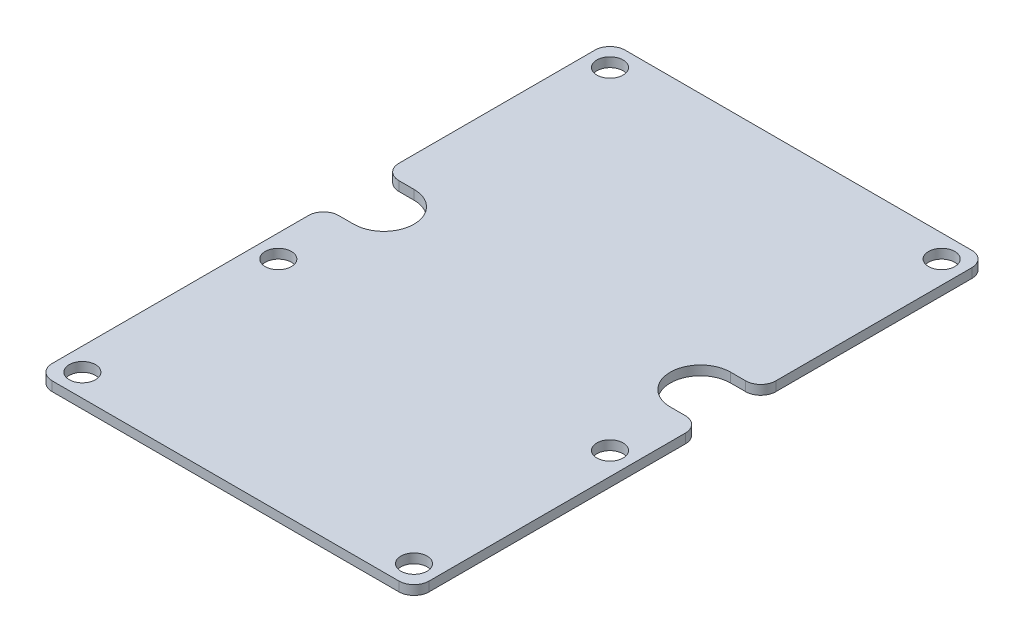
SolidWorks part; units mm, degrees
ref_plane "Front Plane" through (0, 0, 0) normal (0, 0, 1) x (1, 0, 0)
ref_plane "Top Plane" through (0, 0, 0) normal (0, 1, 0) x (1, 0, 0)
ref_plane "Right Plane" through (0, 0, 0) normal (1, 0, 0) x (0, 0, -1)
sketch "Sketch1" plane through (0, 0, 0) normal (0, 1, 0) x (1, 0, 0)
  line L0 (-25.4, -13.97) -> (-25.4, 19.05) construction
  line L1 (22.86, -11.43) -> (-22.86, -11.43) construction
  line L2 (22.86, -11.43) -> (22.86, 11.43) construction
  line L3 (22.86, 11.43) -> (-22.86, 11.43) construction
  line L4 (-22.86, -11.43) -> (-22.86, 11.43) construction
  line L5 (22.86, -11.43) -> (-22.86, 11.43) construction
  line L6 (22.86, 11.43) -> (-22.86, -11.43) construction
  line L7 (-21.59, -12.7) -> (-24.13, -12.7) construction
  line L8 (-21.59, -12.7) -> (-21.59, 12.7) construction
  line L9 (-21.59, 12.7) -> (-24.13, 12.7) construction
  line L10 (-24.13, -12.7) -> (-24.13, 12.7) construction
  line L11 (-21.59, -12.7) -> (-24.13, 12.7) construction
  line L12 (-21.59, 12.7) -> (-24.13, -12.7) construction
  line L13 (24.13, -12.7) -> (21.59, -12.7) construction
  line L14 (24.13, -12.7) -> (24.13, 12.7) construction
  line L15 (24.13, 12.7) -> (21.59, 12.7) construction
  line L16 (21.59, -12.7) -> (21.59, 12.7) construction
  line L17 (24.13, -12.7) -> (21.59, 12.7) construction
  line L18 (24.13, 12.7) -> (21.59, -12.7) construction
  line L19 (-25.4, 19.05) -> (18.415, 19.05) construction
  line L20 (18.415, 19.05) -> (25.4, 12.065) construction
  line L21 (25.4, 12.065) -> (25.4, -13.97) construction
  line L22 (25.4, -13.97) -> (-25.4, -13.97) construction
  line L23 (25.4, 12.065) -> (25.4, 19.05) construction
  line L24 (25.4, 19.05) -> (18.415, 19.05) construction
  point P0 (0, 0)
  point P6 (22.86, 0)
  point P7 (-22.86, -11.43)
  point P8 (22.86, -11.43)
  point P10 (-22.86, -8.89)
  point P11 (22.86, -8.89)
  point P12 (-22.86, -6.35)
  point P13 (22.86, -6.35)
  point P14 (-22.86, -3.81)
  point P15 (22.86, -3.81)
  point P16 (-22.86, -1.27)
  point P17 (22.86, -1.27)
  point P18 (-22.86, 1.27)
  point P19 (22.86, 1.27)
  point P20 (-22.86, 3.81)
  point P21 (22.86, 3.81)
  point P22 (-22.86, 6.35)
  point P23 (22.86, 6.35)
  point P24 (-22.86, 8.89)
  point P25 (22.86, 8.89)
  point P26 (-22.86, 11.43)
  point P27 (22.86, 11.43)
  point P28 (-22.86, 0)
  dimension "D1" = 22.86
  dimension "D2" = 45.72
  dimension "D4" = 2.54
  dimension "D5" = 25.4
  dimension "D6" = 2.54
  dimension "D7" = 2.54
  dimension "D8" = 2.54
  dimension "D9" = 7.62
  dimension "D10" = 0.635
  dimension "D3" = 10
sketch "Sketch2" plane through (0, 0, 0) normal (0, 1, 0) x (1, 0, 0)
  line L8 (-24.384, 12.954) -> (-24.384, -12.954)
  line L9 (-24.384, -12.954) -> (-21.336, -12.954)
  line L10 (-21.336, -12.954) -> (-21.336, 12.954)
  line L11 (-21.336, 12.954) -> (-24.384, 12.954)
  line L12 (-24.384, 12.954) -> (-24.384, -12.954) construction
  line L13 (-24.384, -12.954) -> (-21.336, -12.954) construction
  line L14 (-21.336, -12.954) -> (-21.336, 12.954) construction
  line L15 (-21.336, 12.954) -> (-24.384, 12.954) construction
  line L20 (21.336, -12.954) -> (24.384, -12.954)
  line L21 (24.384, -12.954) -> (24.384, 12.954)
  line L22 (24.384, 12.954) -> (21.336, 12.954)
  line L23 (21.336, 12.954) -> (21.336, -12.954)
  line L24 (21.336, -12.954) -> (24.384, -12.954) construction
  line L25 (24.384, -12.954) -> (24.384, 12.954) construction
  line L26 (24.384, 12.954) -> (21.336, 12.954) construction
  line L27 (21.336, 12.954) -> (21.336, -12.954) construction
  line L34 (-25.781, -14.351) -> (25.781, -14.351)
  line L35 (25.781, -14.351) -> (25.781, 12.2228)
  line L36 (25.781, 12.2228) -> (18.5728, 19.431)
  line L37 (18.5728, 19.431) -> (-25.781, 19.431)
  line L38 (-25.781, 19.431) -> (-25.781, -14.351)
  line L39 (-25.781, -14.351) -> (25.781, -14.351) construction
  line L40 (25.781, -14.351) -> (25.781, 12.2228) construction
  line L41 (25.781, 12.2228) -> (18.5728, 19.431) construction
  line L42 (18.5728, 19.431) -> (-25.781, 19.431) construction
  line L43 (-25.781, 19.431) -> (-25.781, -14.351) construction
  dimension "D1" = 0.254
  dimension "D2" = 0.254
  dimension "D3" = 0.381
sketch "Sketch3" plane through (0, 0, 0) normal (0, 1, 0) x (1, 0, 0)
  line L0 (24.13, 12.7) -> (21.59, 12.7) construction
  line L1 (21.59, -12.7) -> (21.59, 12.7) construction
  line L2 (24.13, -12.7) -> (24.13, 12.7) construction
  line L3 (24.13, -12.7) -> (21.59, -12.7) construction
  line L4 (-21.59, -12.7) -> (-24.13, -12.7) construction
  line L5 (-24.13, -12.7) -> (-24.13, 12.7) construction
  line L6 (-21.59, -12.7) -> (-21.59, 12.7) construction
  line L7 (-21.59, 12.7) -> (-24.13, 12.7) construction
  line L8 (24.13, 12.7) -> (21.59, 12.7) construction
  line L9 (21.59, -12.7) -> (21.59, 12.7) construction
  line L10 (24.13, -12.7) -> (24.13, 12.7) construction
  line L11 (24.13, -12.7) -> (21.59, -12.7) construction
  line L12 (-21.59, -12.7) -> (-24.13, -12.7) construction
  line L13 (-24.13, -12.7) -> (-24.13, 12.7) construction
  line L14 (-21.59, -12.7) -> (-21.59, 12.7) construction
  line L15 (-21.59, 12.7) -> (-24.13, 12.7) construction
  line L16 (-21.59, 43.18) -> (-24.13, 43.18) construction
  line L17 (-24.13, 43.18) -> (-24.13, 68.58) construction
  line L18 (-21.59, 68.58) -> (-24.13, 68.58) construction
  line L19 (-21.59, 43.18) -> (-21.59, 68.58) construction
  line L20 (24.13, 43.18) -> (24.13, 68.58) construction
  line L21 (24.13, 68.58) -> (21.59, 68.58) construction
  line L22 (21.59, 43.18) -> (21.59, 68.58) construction
  line L23 (24.13, 43.18) -> (21.59, 43.18) construction
  line L24 (-21.59, -12.7) -> (-21.59, 43.18) construction
  line L25 (0, 0) -> (0, 69.85) construction
  line L27 (-29.21, 109.22) -> (29.21, 109.22) construction
  line L28 (-29.21, 109.22) -> (-29.21, 30.48) construction
  line L29 (-29.21, 30.48) -> (29.21, 30.48) construction
  line L30 (29.21, 109.22) -> (29.21, 30.48) construction
  line L31 (-29.21, 109.22) -> (29.21, 30.48) construction
  line L32 (-29.21, 30.48) -> (29.21, 109.22) construction
  dimension "D2" = 55.88
  dimension "D3" = 58.42
  dimension "D4" = 78.74
  dimension "D5" = 12.7
  dimension "D1" = 2
sketch "Sketch4" plane through (0, 0, 0) normal (0, 1, 0) x (1, 0, 0)
  line L0 (0, 0) -> (0, 69.85) construction
  line L1 (-29.21, 76.2) -> (29.21, 76.2)
  line L2 (-31.75, 73.66) -> (-31.75, -17.78) construction
  line L3 (-29.21, -20.32) -> (29.21, -20.32)
  line L4 (31.75, 73.66) -> (31.75, -17.78) construction
  line L5 (-31.75, 76.2) -> (31.75, -20.32) construction
  line L6 (-31.75, -20.32) -> (31.75, 76.2) construction
  line L10 (24.13, 68.58) -> (21.59, 68.58) construction
  line L11 (24.13, -12.7) -> (24.13, 12.7) construction
  line L12 (24.13, -12.7) -> (21.59, -12.7) construction
  line L13 (24.13, 43.18) -> (24.13, 35.56) construction
  line L14 (24.13, 35.56) -> (24.13, 30.48) construction
  line L15 (-29.21, 30.48) -> (29.21, 30.48) construction
  line L16 (24.13, 35.56) -> (29.21, 35.56) construction
  line L18 (29.21, 109.22) -> (29.21, 30.48) construction
  line L19 (26.67, 35.56) -> (26.67, 30.48) construction
  line L20 (29.21, 38.1) -> (26.67, 38.1)
  line L21 (26.67, 27.94) -> (29.21, 27.94)
  line L22 (0, 0) -> (0, 69.85) construction
  line L23 (-26.67, 27.94) -> (-29.21, 27.94)
  line L24 (-29.21, 38.1) -> (-26.67, 38.1)
  line L25 (-31.75, 73.66) -> (-31.75, 40.64)
  line L26 (-31.75, 25.4) -> (-31.75, -17.78)
  line L27 (31.75, -17.78) -> (31.75, 25.4)
  line L28 (31.75, 40.64) -> (31.75, 73.66)
  arc A0 (-31.75, -17.78) -> (-29.21, -20.32) centre (-29.21, -17.78) ccw
  arc A1 (29.21, -20.32) -> (31.75, -17.78) centre (29.21, -17.78) ccw
  arc A2 (29.21, 76.2) -> (31.75, 73.66) centre (29.21, 73.66) cw
  arc A3 (-29.21, 76.2) -> (-31.75, 73.66) centre (-29.21, 73.66) ccw
  arc A4 (26.67, 38.1) -> (26.67, 27.94) centre (26.67, 33.02) ccw
  arc A5 (-26.67, 38.1) -> (-26.67, 27.94) centre (-26.67, 33.02) cw
  arc A6 (29.21, 27.94) -> (31.75, 25.4) centre (29.21, 25.4) cw
  arc A7 (29.21, 38.1) -> (31.75, 40.64) centre (29.21, 40.64) ccw
  arc A8 (-31.75, 25.4) -> (-29.21, 27.94) centre (-29.21, 25.4) cw
  arc A9 (-29.21, 38.1) -> (-31.75, 40.64) centre (-29.21, 40.64) cw
  point P0 (0, 27.94)
  point P48 (31.75, 27.94)
  point P51 (31.75, 38.1)
  point P54 (-31.75, 27.94)
  point P57 (-31.75, 38.1)
  point P58 (0, 0)
  dimension "D4" = 2.54
  dimension "D6" = 2.54
  dimension "D1" = 7.62
  dimension "D2" = 7.62
  dimension "D3" = 7.62
  dimension "D5" = 10.16
extrude "Boss-Extrude1" add sketch "Sketch4" against normal blind 1.5875
sketch "Sketch5" plane through (0, 0, 0) normal (0, 1, 0) x (1, 0, 0)
  line L0 (-31.0061, 75.4561) -> (-27.94, 72.39) construction
  line L1 (-31.75, 73.66) -> (-31.75, 40.64) construction
  line L2 (0, 76.2) -> (0, -20.32) construction
  line L3 (29.21, 76.2) -> (-29.21, 76.2) construction
  line L4 (-29.21, -20.32) -> (29.21, -20.32) construction
  line L5 (31.75, 27.94) -> (-31.75, 27.94) construction
  line L6 (31.75, -17.78) -> (31.75, 25.4) construction
  line L7 (-31.75, 25.4) -> (-31.75, -17.78) construction
  line L8 (-24.13, 0) -> (24.13, 0) construction
  line L9 (-24.13, -12.7) -> (-24.13, 12.7) construction
  line L10 (24.13, -12.7) -> (24.13, 12.7) construction
  arc A0 (-29.21, 76.2) -> (-31.75, 73.66) centre (-29.21, 73.66) ccw construction
  circle A1 centre (-27.94, 72.39) radius 2.2098
  circle A2 centre (27.94, 72.39) radius 2.2098
  circle A3 centre (-27.94, -16.51) radius 2.2098
  circle A4 centre (27.94, -16.51) radius 2.2098
  circle A5 centre (-27.94, 16.51) radius 2.2098
  circle A6 centre (27.94, 16.51) radius 2.2098
  point P21 (0, 27.94)
  point P23 (0, 27.94)
  dimension "D1" = 4.4196
  dimension "D2" = 3.81
extrude "Cut-Extrude1" cut sketch "Sketch5" against normal through all
